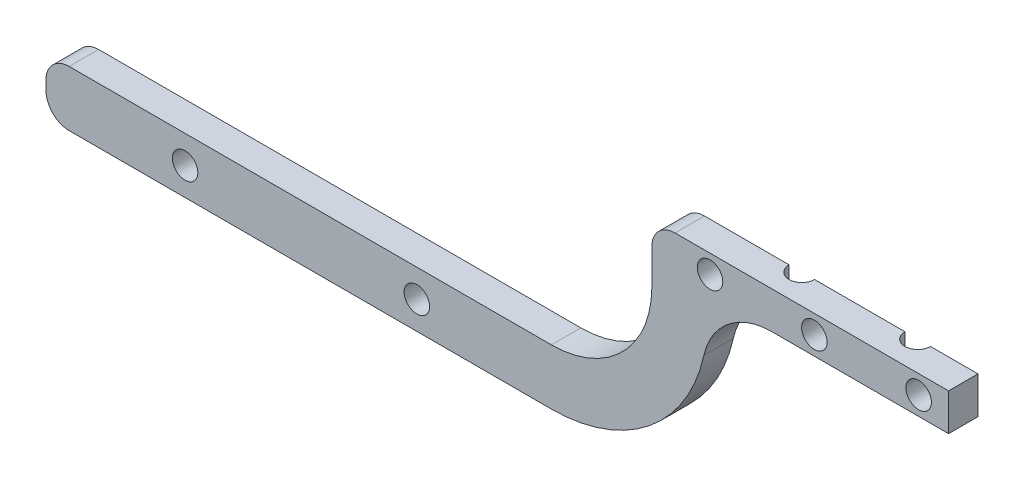
SolidWorks part; units mm, degrees
ref_plane "Front Plane" through (0, 0, 0) normal (0, 0, 1) x (1, 0, 0)
ref_plane "Top Plane" through (0, 0, 0) normal (0, 1, 0) x (1, 0, 0)
ref_plane "Right Plane" through (0, 0, 0) normal (1, 0, 0) x (0, 0, -1)
sketch "Sketch1" plane through (0, 0, 0) normal (0, 0, 1) x (1, 0, 0)
  line L0 (0, 0) -> (-64, 0)
  line L1 (-64, 0) -> (-64, -12.5522)
  line L2 (0, 0) -> (0, -8)
  line L3 (0, -8) -> (-52, -8)
  line L4 (-85.6878, -34.24) -> (-194.6878, -34.24)
  line L5 (-194.6878, -34.24) -> (-194.6878, -46.24)
  line L6 (-194.6878, -46.24) -> (-85.6878, -46.24)
  line L7 (-52, -12.5522) -> (-52, -8)
  arc A0 (-64, -12.5522) -> (-85.6878, -34.24) centre (-85.6878, -12.5522) cw
  arc A2 (-85.6878, -46.24) -> (-52, -12.5522) centre (-85.6878, -12.5522) ccw
  dimension "D4" = 4.5522
  dimension "D1" = 64
  dimension "D2" = 8
  dimension "D3" = 26.24
  dimension "D5" = 109
  dimension "D6" = 12
extrude "Boss-Extrude1" add sketch "Sketch1" along normal blind 6.35
fillet "Fillet1" radius 5 3 edges at (-64, 0, 3.175) (-194.6878, -46.24, 3.175) (-194.6878, -34.24, 3.175)
sketch "Sketch3" plane through (0, 0, 0) normal (0, 1, 0) x (1, 0, 0)
  line L0 (0, -3.175) -> (-59, -3.175) construction
  line L1 (0, -6.35) -> (0, 0) construction
  line L2 (-59, 0) -> (-59, -6.35) construction
  line L3 (0, 0) -> (-59, 0) construction
  circle A0 centre (-13, 0) radius 2.75
  circle A1 centre (-38, 0) radius 2.75
  point P8 (0, 0)
  dimension "D1" = 5.5
  dimension "D2" = 5.5
  dimension "D3" = 25
  dimension "D4" = 13
fillet "Fillet2" radius 15 1 edges at (-52, -8, 3.175)
sketch "Sketch4" plane through (0, 0, 6.35) normal (0, 0, 1) x (1, 0, 0)
  line L0 (-181.7526, -34.24) -> (-181.7526, -46.24) construction
  line L1 (-85.6878, -34.24) -> (-189.6878, -34.24) construction
  line L2 (-189.6878, -46.24) -> (-85.6878, -46.24) construction
  line L3 (-181.7526, -40.24) -> (-194.6878, -40.24) construction
  line L4 (-194.6878, -39.24) -> (-194.6878, -41.24) construction
  line L5 (-66.4979, -40.24) -> (-181.7526, -40.24) construction
  line L6 (0, -4) -> (-63.899, -4) construction
  line L7 (0, -8) -> (0, 0) construction
  line L8 (-6.4525, 0) -> (-6.4525, -8) construction
  line L9 (0, 0) -> (-59, 0) construction
  line L10 (-38.1342, -8) -> (0, -8) construction
  line L11 (-28.9525, 0) -> (-28.9525, -8) construction
  line L12 (-51.4525, 0) -> (-51.4525, -16.0991) construction
  arc A0 (-85.6878, -46.24) -> (-52.7848, -19.7812) centre (-85.6878, -12.5522) ccw construction
  circle A1 centre (-164.6878, -40.24) radius 2.75
  circle A2 centre (-114.6878, -40.24) radius 2.75
  arc A3 (-59, 0) -> (-64, -5) centre (-59, -5) ccw construction
  arc A4 (-38.1342, -8) -> (-52.7848, -19.7812) centre (-38.1342, -23) ccw construction
  circle A5 centre (-6.4525, -4) radius 2.75
  circle A6 centre (-28.9525, -4) radius 2.75
  circle A7 centre (-51.4525, -4) radius 2.75
  dimension "D1" = 5.5
  dimension "D2" = 5.5
  dimension "D5" = 5.5
  dimension "D6" = 5.5
  dimension "D7" = 5.5
  dimension "D3" = 50
  dimension "D4" = 30
  dimension "D8" = 22.5
  dimension "D9" = 22.5
extrude "Cut-Extrude2" cut sketch "Sketch4" against normal blind 10
extrude "Cut-Extrude3" cut sketch "Sketch3" against normal up to next
